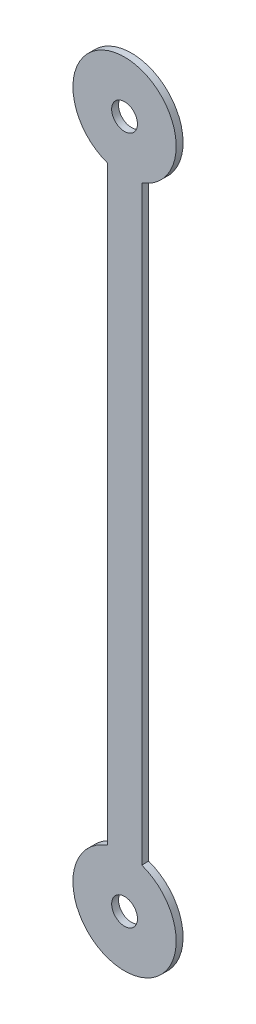
SolidWorks part; units mm, degrees
material "3.0517 (EN-AW 3003)"
ref_plane "Front Plane" through (0, 0, 0) normal (0, 0, 1) x (1, 0, 0)
ref_plane "Top Plane" through (0, 0, 0) normal (0, 1, 0) x (1, 0, 0)
ref_plane "Right Plane" through (0, 0, 0) normal (1, 0, 0) x (0, 0, -1)
sketch "Sketch1" plane through (0, 0, 0) normal (0, 0, 1) x (1, 0, 0)
  line L0 (0, 10) -> (0, -10) construction
  line L1 (-0.5, 8.5858) -> (-0.5, -8.5858)
  line L2 (0.5, 8.5858) -> (0.5, -8.5858)
  line L3 (-0.5, 10) -> (-0.5, -10) construction
  line L4 (0.5, 10) -> (0.5, -10) construction
  circle A0 centre (0, 10) radius 0.375
  arc A1 (0.5, 8.5858) -> (-0.5, 8.5858) centre (0, 10) ccw
  arc A2 (-0.5, -8.5858) -> (0.5, -8.5858) centre (0, -10) ccw
  circle A3 centre (0, -10) radius 0.375
  dimension "D2" = 0.75
  dimension "D3" = 3
  dimension "D4" = 0.5
  dimension "D5" = 0.5
  dimension "D1" = 20
extrude "Boss-Extrude1" add sketch "Sketch1" along normal mid plane 0.2
sketch "Sketch2" plane through (0, 0, 0) normal (0, 0, 1) x (1, 0, 0)
  line L0 (-0.75, 8.701) -> (0.75, 8.701)
  line L1 (0.75, -8.701) -> (-0.75, -8.701)
  line L9 (-0.75, 8.5858) -> (-0.75, -8.5858)
  line L10 (-0.75, 8.701) -> (-0.75, -8.701)
  line L12 (0.75, -8.5858) -> (0.75, 8.5858)
  line L13 (0.75, -8.701) -> (0.75, 8.701)
  arc A0 (0.5, 8.5858) -> (-0.5, 8.5858) centre (0, 10) ccw construction
  arc A1 (0.5, 8.5858) -> (-0.5, 8.5858) centre (0, 10) ccw construction
  arc A2 (-0.5, -8.5858) -> (0.5, -8.5858) centre (0, -10) ccw construction
  arc A3 (-0.5, -8.5858) -> (0.5, -8.5858) centre (0, -10) ccw construction
  dimension "D1" = 0.25
  dimension "D2" = 0.25
extrude "Boss-Extrude2" [suppressed] add sketch "Sketch2" along normal mid plane 0.6
